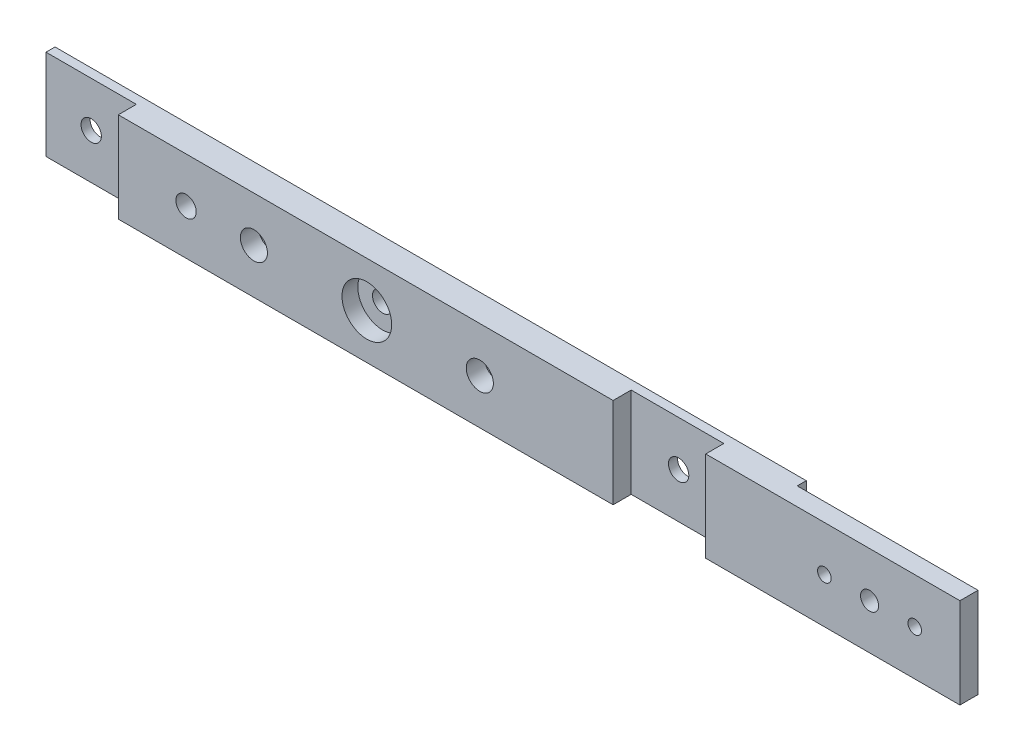
SolidWorks part; units mm, degrees
ref_plane "Plan de face" through (0, 0, 0) normal (0, 0, 1) x (1, 0, 0)
ref_plane "Plan de dessus" through (0, 0, 0) normal (0, 1, 0) x (1, 0, 0)
ref_plane "Plan de droite" through (0, 0, 0) normal (1, 0, 0) x (0, 0, -1)
sketch "Esquisse1" plane through (0, 0, 0) normal (0, 0, 1) x (1, 0, 0)
  line L1 (-227.0899, 56.9648) -> (185.4101, 56.9648)
  line L2 (-227.0899, 56.9648) -> (-227.0899, 16.9648)
  line L3 (-227.0899, 16.9648) -> (185.4101, 16.9648)
  line L4 (185.4101, 56.9648) -> (185.4101, 16.9648)
  dimension "D1" = 412.5
  dimension "D2" = 40
extrude "Boss.-Extru.1" add sketch "Esquisse1" along normal blind 12
sketch "Esquisse2" plane through (0, 0, 12) normal (0, 0, 1) x (1, 0, 0)
  line L0 (-227.0899, 36.9648) -> (185.4101, 36.9648) construction
  line L1 (-227.0899, 56.9648) -> (-227.0899, 16.9648) construction
  line L2 (185.4101, 16.9648) -> (185.4101, 56.9648) construction
  line L4 (185.4101, 56.9648) -> (-227.0899, 56.9648) construction
  circle A0 centre (-207.0899, 36.9648) radius 4.5
  circle A1 centre (-157.0899, 36.9648) radius 4.5
  circle A3 centre (52.9101, 36.9648) radius 4.5
  dimension "D1" = 20
  dimension "D2" = 9
  dimension "D4" = 9
  dimension "D8" = 9
  dimension "D14" = 20
  dimension "D3" = 70
  dimension "D7" = 132.5
extrude "Enlèv. mat.-Extru.1" cut sketch "Esquisse2" against normal through all
sketch "Esquisse3" plane through (0, 0, 12) normal (0, 0, 1) x (1, 0, 0)
  line L0 (-227.0899, 36.9648) -> (-15.0667, 36.9648) construction
  line L1 (-227.0899, 56.9648) -> (-227.0899, 16.9648) construction
  line L2 (185.4101, 56.9648) -> (-227.0899, 56.9648) construction
  circle A0 centre (-77.0899, 36.9648) radius 11
  dimension "D1" = 22
  dimension "D3" = 20
  dimension "D2" = 150
extrude "Enlèv. mat.-Extru.2" cut sketch "Esquisse3" against normal blind 7
sketch "Esquisse4" plane through (0, 0, 12) normal (0, 0, 1) x (1, 0, 0)
  line L0 (-227.0899, 16.9648) -> (185.4101, 16.9648) construction
  line L1 (-227.0899, 56.9648) -> (-187.0899, 56.9648)
  line L2 (-227.0899, 56.9648) -> (-227.0899, 16.9648)
  line L3 (-227.0899, 16.9648) -> (-187.0899, 16.9648)
  line L4 (-187.0899, 56.9648) -> (-187.0899, 16.9648)
  line L5 (185.4101, 16.9648) -> (185.4101, 56.9648) construction
  line L10 (185.4101, 56.9648) -> (-227.0899, 56.9648) construction
  line L11 (72.9101, 56.9648) -> (72.9101, 16.9648) construction
  line L12 (-77.0899, 36.9648) -> (-77.0899, 56.9648) construction
  line L14 (72.9101, 56.9648) -> (31.9101, 56.9648)
  line L15 (72.9101, 56.9648) -> (72.9101, 16.9648)
  line L16 (72.9101, 16.9648) -> (31.9101, 16.9648)
  line L17 (31.9101, 56.9648) -> (31.9101, 16.9648)
  dimension "D1" = 40
  dimension "D2" = 112.5
  dimension "D3" = 41
extrude "Enlèv. mat.-Extru.3" cut sketch "Esquisse4" against normal blind 8
sketch "Esquisse5" plane through (0, 0, 12) normal (0, 0, 1) x (1, 0, 0)
  line L0 (-227.0899, 36.9648) -> (225.4101, 36.9648) construction
  line L3 (-187.0899, 16.9648) -> (-187.0899, 56.9648) construction
  line L4 (-187.0899, 56.9648) -> (-227.0899, 56.9648) construction
  line L5 (31.9101, 56.9648) -> (31.9101, 16.9648) construction
  circle A0 centre (-127.0899, 36.9648) radius 6
  circle A1 centre (-27.0899, 36.9648) radius 6
  dimension "D1" = 12
  dimension "D2" = 12
  dimension "D4" = 59
  dimension "D3" = 60
  dimension "D5" = 20
extrude "Enlèv. mat.-Extru.5" cut sketch "Esquisse5" against normal blind 8
sketch "Esquisse6" plane through (0, 0, 0) normal (0, 0, -1) x (-1, 0, 0)
  line L0 (227.0899, 16.9648) -> (-185.4101, 16.9648) construction
  line L1 (-185.4101, 56.9648) -> (-105.4101, 56.9648)
  line L2 (-185.4101, 56.9648) -> (-185.4101, 16.9648)
  line L3 (-185.4101, 16.9648) -> (-105.4101, 16.9648)
  line L4 (-105.4101, 56.9648) -> (-105.4101, 16.9648)
  dimension "D1" = 80
extrude "Enlèv. mat.-Extru.6" cut sketch "Esquisse6" against normal blind 4
sketch "Esquisse7" plane through (0, 0, 4) normal (0, 0, -1) x (-1, 0, 0)
  line L0 (-185.4101, 36.9648) -> (-108.2231, 36.9648) construction
  line L1 (-185.4101, 56.9648) -> (-185.4101, 16.9648) construction
  line L2 (-108.2231, 36.9648) -> (-108.2231, 37.262) construction
  circle A0 centre (-165.4101, 36.9648) radius 3
  circle A1 centre (-125.4101, 36.9648) radius 3
  dimension "D1" = 6
  dimension "D2" = 6
  dimension "D4" = 40
  dimension "D3" = 20
extrude "Enlèv. mat.-Extru.7" cut sketch "Esquisse7" against normal through all
sketch "Esquisse8" plane through (0, 0, 4) normal (0, 0, -1) x (-1, 0, 0)
  line L0 (-185.4101, 36.9648) -> (-108.0454, 36.9648) construction
  line L1 (-185.4101, 56.9648) -> (-185.4101, 16.9648) construction
  line L2 (-185.4101, 16.9648) -> (-185.4101, 56.9648) construction
  circle A0 centre (-145.4101, 36.9648) radius 4
  dimension "D1" = 8
  dimension "D2" = 40
extrude "Enlèv. mat.-Extru.8" cut sketch "Esquisse8" against normal through all
sketch "Esquisse9" plane through (0, 0, 5) normal (0, 0, 1) x (1, 0, 0)
  circle A0 centre (-77.0899, 36.9648) radius 4.5
  dimension "D1" = 9
extrude "Enlèv. mat.-Extru.9" cut sketch "Esquisse9" against normal through all
